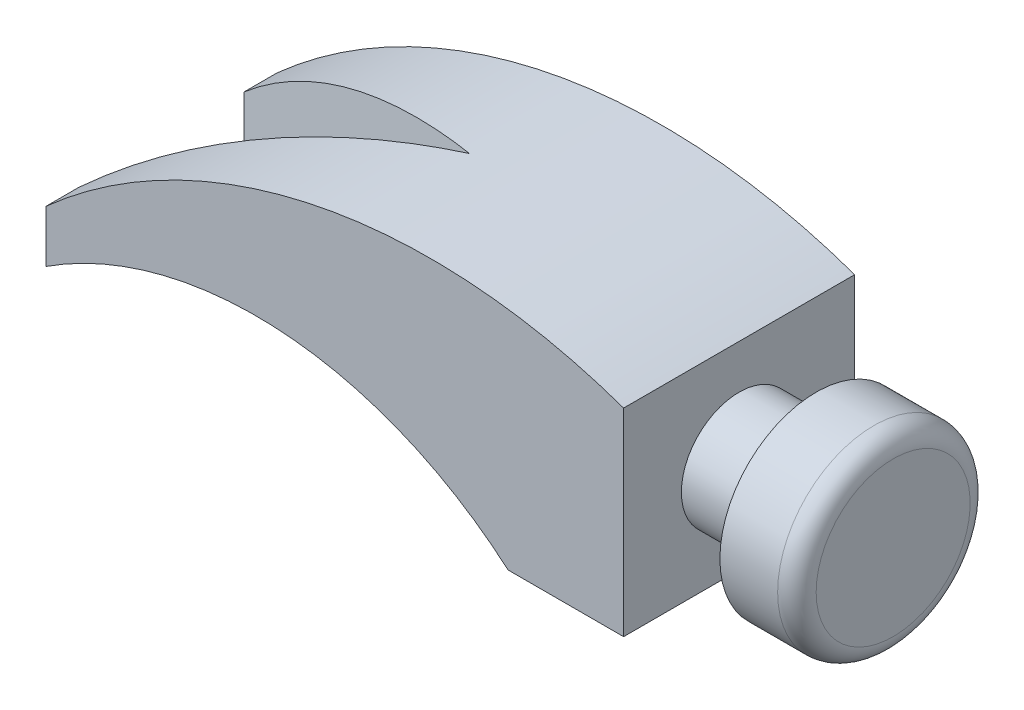
SolidWorks part; units mm, degrees
ref_plane "Front Plane" through (0, 0, 0) normal (0, 0, 1) x (1, 0, 0)
ref_plane "Top Plane" through (0, 0, 0) normal (0, 1, 0) x (1, 0, 0)
ref_plane "Right Plane" through (0, 0, 0) normal (1, 0, 0) x (0, 0, -1)
sketch "Sketch1" plane through (0, 0, 0) normal (0, 0, 1) x (1, 0, 0)
  line L7 (49.1248, -30.034) -> (49.1248, 21.3874)
  line L13 (19.1248, -30.034) -> (49.1248, -30.034)
  line L15 (-100.8752, -21.7638) -> (-100.8752, -8.2306)
  arc A0 (49.1248, 21.3874) -> (-100.8752, -8.2306) centre (-0.8752, -120.034) ccw
  arc A1 (19.1248, -30.034) -> (-100.8752, -21.7638) centre (-46.3683, -105.6029) ccw
  point P14 (-36.3683, -30.6029)
extrude "Boss-Extrude1" add sketch "Sketch1" along normal blind 60
ref_plane "Plane1" through (0, 0, 30) normal (0, 0, 1) x (1, 0, 0)
sketch "Sketch3" plane through (0, 0, 30) normal (0, 0, 1) x (1, 0, 0)
  line L0 (49.1248, -30.034) -> (49.1248, -5.034) construction
  line L1 (49.1248, -30.034) -> (49.1248, 21.3874) construction
  line L2 (49.1248, -5.034) -> (121.2837, -5.034) construction
  line L3 (49.1248, -5.034) -> (49.1248, 9.966)
  line L4 (49.1248, 9.966) -> (69.1248, 9.966)
  line L5 (69.1248, 9.966) -> (69.1248, 19.966)
  line L6 (69.1248, 19.966) -> (84.1248, 19.966)
  line L7 (89.1248, 14.966) -> (89.1248, -5.034) construction
  line L8 (49.1248, -5.034) -> (89.1248, -5.034) construction
  line L9 (89.1248, 14.966) -> (89.1248, -5.034)
  line L10 (49.1248, -5.034) -> (89.1248, -5.034)
  arc A0 (89.1248, 14.966) -> (84.1248, 19.966) centre (84.1248, 14.966) ccw
revolve "Revolve1" add sketch "Sketch3" angle 360 about L10
sketch "Sketch5" plane through (0, 0, 0) normal (0, 1, 0) x (1, 0, 0)
  line L0 (-100.8752, -8.5479) -> (-100.8752, -51.4197)
  line L3 (-20.8752, -30) -> (-100.8752, -8.5479)
  line L6 (-100.8752, -60) -> (-100.8752, 0) construction
  line L7 (-20.8752, -30) -> (-100.8752, -51.4197)
extrude "Cut-Extrude1" cut sketch "Sketch5" against normal blind 50 contours L0 L7 L3
sketch "Sketch6" plane through (0, 0, 0) normal (0, -1, 0) x (1, 0, 0)
  line L0 (-90.8299, 48.7301) -> (-20.8752, 30)
  line L1 (-20.8752, 30) -> (-90.8299, 11.2415)
  line L2 (-90.8299, 11.2415) -> (-90.8299, 48.7301)
extrude "Cut-Extrude2" cut sketch "Sketch6" against normal blind 50
